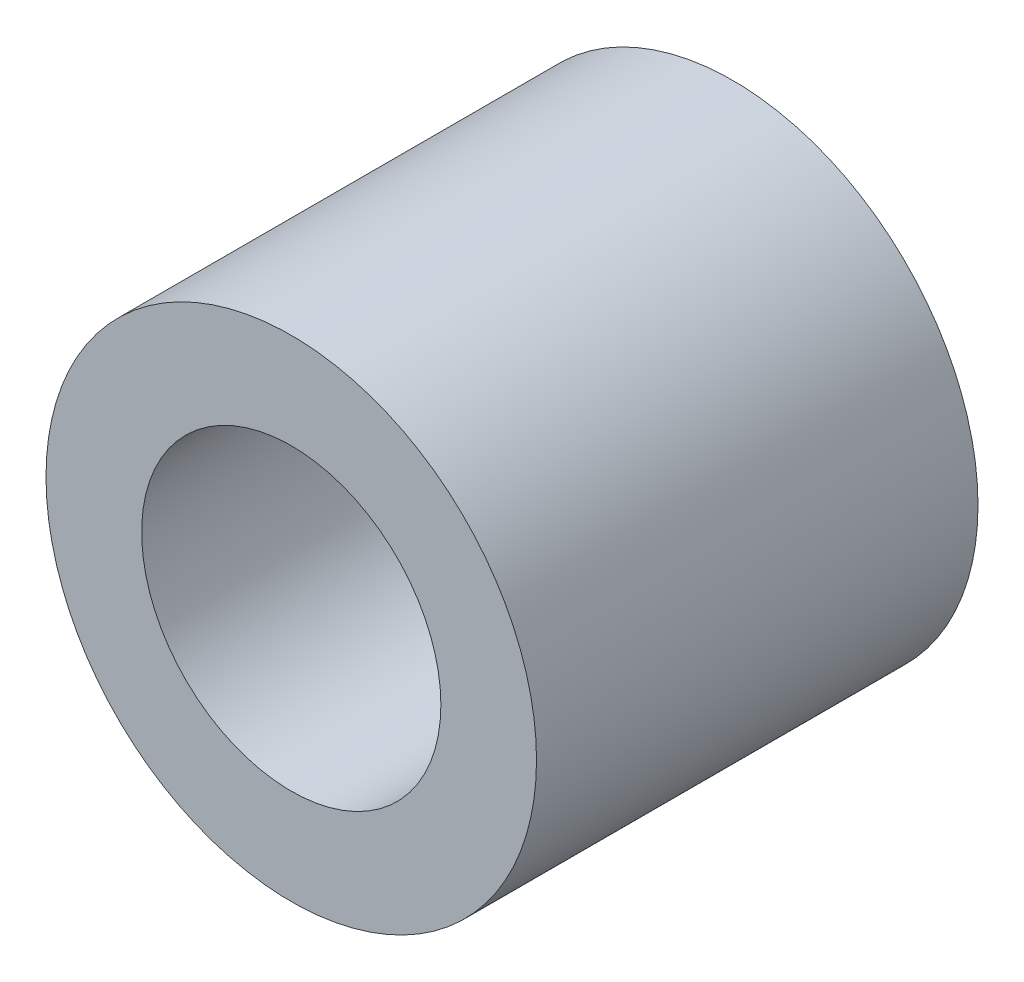
SolidWorks part; units mm, degrees
ref_plane "正面" through (0, 0, 0) normal (0, 0, 1) x (1, 0, 0)
ref_plane "平面" through (0, 0, 0) normal (0, 1, 0) x (1, 0, 0)
ref_plane "右側面" through (0, 0, 0) normal (1, 0, 0) x (0, 0, -1)
sketch "ｽｹｯﾁ1" plane through (0, 0, 0) normal (0, 0, 1) x (1, 0, 0)
  circle A0 centre (0, 0) radius 5
  circle A1 centre (0, 0) radius 3.05
  dimension "D1" = 6.1
  dimension "D2" = 10
extrude "ﾎﾞｽ - 押し出し1" add sketch "ｽｹｯﾁ1" along normal blind 9
